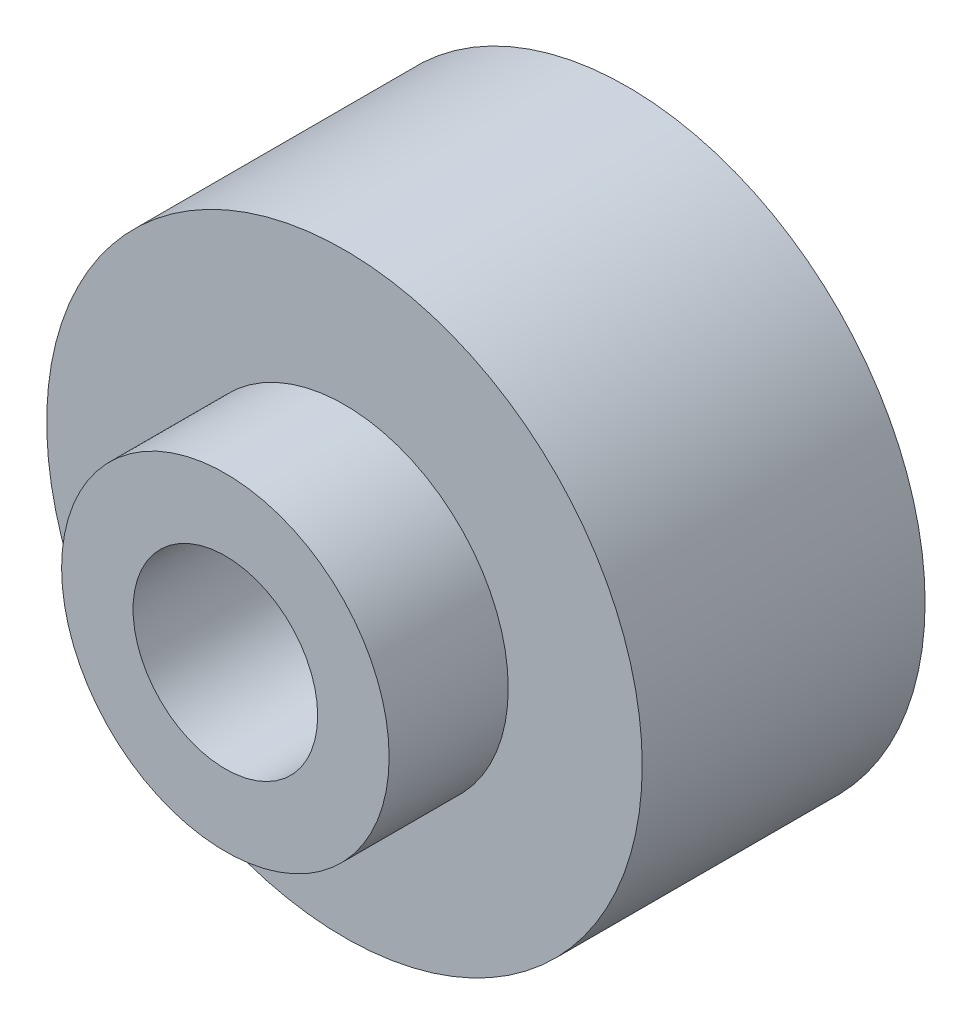
SolidWorks part; units mm, degrees
ref_plane "前视基准面" through (0, 0, 0) normal (0, 0, 1) x (1, 0, 0)
ref_plane "上视基准面" through (0, 0, 0) normal (0, 1, 0) x (1, 0, 0)
ref_plane "右视基准面" through (0, 0, 0) normal (1, 0, 0) x (0, 0, -1)
sketch "草图1" plane through (0, 0, 0) normal (0, 0, 1) x (1, 0, 0)
  circle A0 centre (0, 0) radius 5
  circle A1 centre (0, 0) radius 1.55
  dimension "D1" = 10
  dimension "D2" = 3.1
extrude "凸台-拉伸1" add sketch "草图1" along normal blind 4.75
sketch "草图2" plane through (0, 0, 4.75) normal (0, 0, 1) x (1, 0, 0)
  circle A0 centre (0, 0) radius 2.75
  circle A1 centre (0, 0) radius 1.55
  dimension "D1" = 5.5
extrude "凸台-拉伸2" add sketch "草图2" along normal blind 2
ref_axis "基准轴1" through (0, 0, 4.75) along (0, 0, -1)
sketch "草图5" plane through (0, 0, 0) normal (0, 1, 0) x (1, 0, 0)
  line L0 (0, -4.75) -> (0, 0) construction
  line L1 (3, 0) -> (1.55, -2)
  line L2 (1.55, -2) -> (0, -2)
  line L3 (0, 0) -> (3, 0)
  line L4 (5, 0) -> (-5, 0) construction
  line L5 (0, -2) -> (0, 0)
  point P0 (3, 0)
  point P2 (-3, -0.0215)
  dimension "D1" = 2
  dimension "D3" = 3
  dimension "D4" = 3
revolve "切除-旋转1" cut sketch "草图5" angle 360 about axis through (0, 0, 4.75) along (0, 0, -1)
